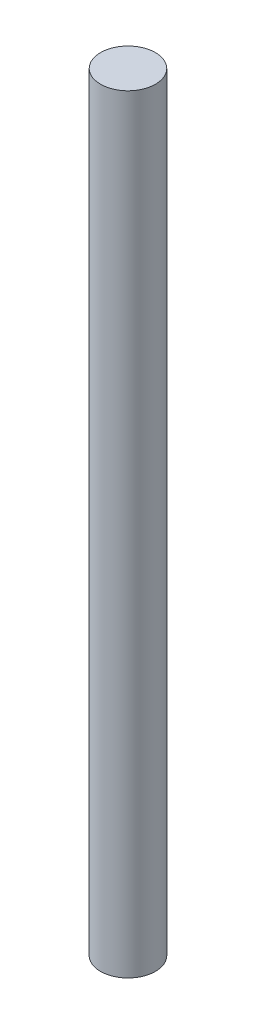
SolidWorks part; units mm, degrees
material "Plain Carbon Steel"
ref_plane "Front Plane" through (0, 0, 0) normal (0, 0, 1) x (1, 0, 0)
ref_plane "Top Plane" through (0, 0, 0) normal (0, 1, 0) x (1, 0, 0)
ref_plane "Right Plane" through (0, 0, 0) normal (1, 0, 0) x (0, 0, -1)
sketch "Sketch1" plane through (0, 0, 0) normal (0, 1, 0) x (1, 0, 0)
  circle A0 centre (0, 0) radius 3.175
  dimension "D1" = 6.35
extrude "Boss-Extrude1" add sketch "Sketch1" along normal blind 88.9
